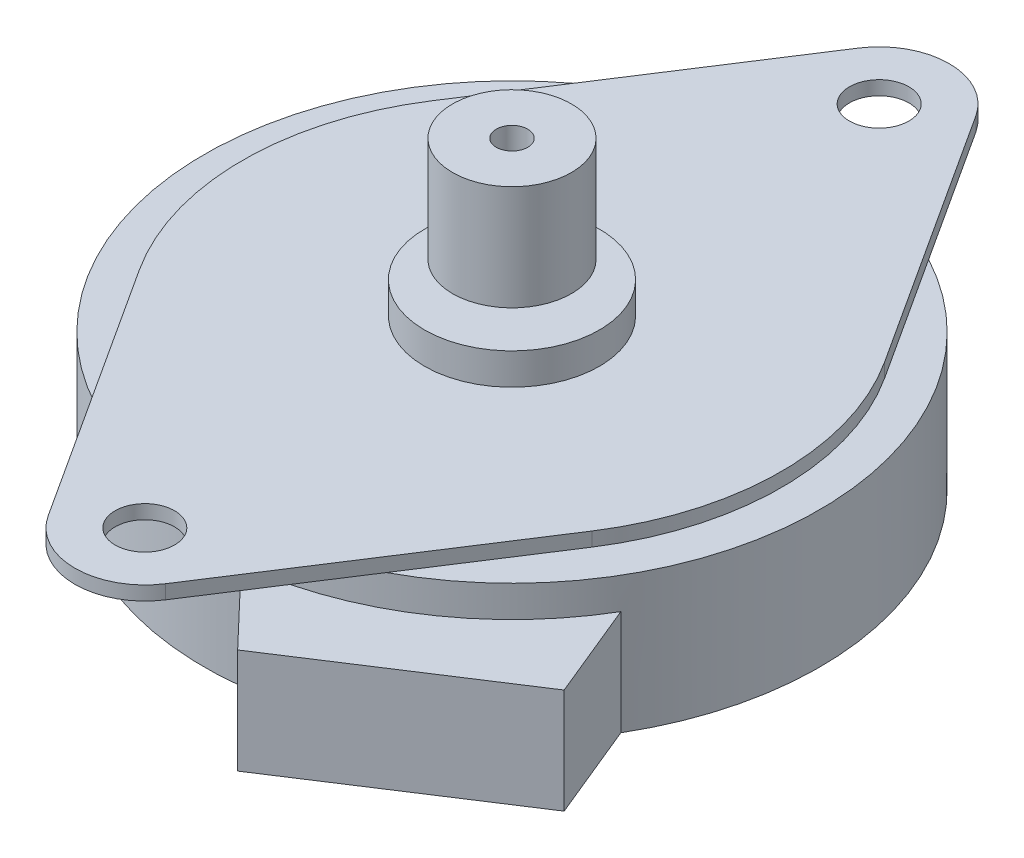
SolidWorks part; units mm, degrees
ref_plane "Piano frontale" through (0, 0, 0) normal (0, 0, 1) x (1, 0, 0)
ref_plane "Piano superiore" through (0, 0, 0) normal (0, 1, 0) x (1, 0, 0)
ref_plane "Piano destro" through (0, 0, 0) normal (1, 0, 0) x (0, 0, -1)
sketch "Schizzo1" plane through (0, 0, 0) normal (0, 1, 0) x (1, 0, 0)
  circle A0 centre (0, 0) radius 17.6
  dimension "D1" = 35.2
extrude "Estrusione-Estrusione1" add sketch "Schizzo1" along normal blind 7.8
sketch "Schizzo2" plane through (0, 7.8, 0) normal (0, 1, 0) x (1, 0, 0)
  line L0 (0, 19.0061) -> (0, -19.0061) construction
  line L1 (-3.3578, -23.1737) -> (-12.9377, -8.3755)
  line L2 (3.3578, -23.1737) -> (12.9377, -8.3755)
  line L3 (3.3578, 23.1737) -> (12.9377, 8.3755)
  line L4 (-3.3578, 23.1737) -> (-12.9377, 8.3755)
  circle A0 centre (0, 21) radius 1.7
  arc A1 (3.3578, 23.1737) -> (-3.3578, 23.1737) centre (0, 21) ccw
  arc A2 (-12.9377, 8.3755) -> (-12.9377, -8.3755) centre (0, 0) ccw
  circle A3 centre (0, -21) radius 1.7
  arc A4 (-3.3578, -23.1737) -> (3.3578, -23.1737) centre (0, -21) ccw
  arc A5 (12.9377, -8.3755) -> (12.9377, 8.3755) centre (0, 0) ccw
  point P18 (0, 0)
  dimension "D2" = 3.4
  dimension "D3" = 8
  dimension "D1" = 21
  dimension "D4" = 2
extrude "Estrusione-Estrusione2" add sketch "Schizzo2" along normal blind 0.8
sketch "Schizzo3" plane through (0, 8.6, 0) normal (0, 1, 0) x (1, 0, 0)
  circle A0 centre (0, 0) radius 5
  dimension "D1" = 10
extrude "Estrusione-Estrusione3" add sketch "Schizzo3" along normal blind 1.8
sketch "Schizzo4" plane through (0, 10.4, 0) normal (0, 1, 0) x (1, 0, 0)
  circle A0 centre (0, 0) radius 0.9
  dimension "D1" = 1.8
extrude "Estrusione-Estrusione4" add sketch "Schizzo4" along normal blind 5
sketch "Schizzo5" plane through (0, 0, 0) normal (0, -1, 0) x (1, 0, 0)
  circle A0 centre (0, 0) radius 2.6
  dimension "D1" = 5.2
extrude "Estrusione-Estrusione5" add sketch "Schizzo5" along normal blind 0.5
sketch "Schizzo6" plane through (0, 0, 0) normal (0, -1, 0) x (1, 0, 0)
  line L0 (0, 0) -> (9.584, 14.7617) construction
  line L1 (6.1007, 21.7923) -> (17.4236, 14.441)
  line L5 (9.584, 14.7617) -> (11.7621, 18.1166) construction
  line L7 (6.1007, 21.7923) -> (1.9938, 17.4867)
  line L8 (17.4236, 14.441) -> (15.1619, 8.9374)
  arc A0 (1.9938, 17.4867) -> (15.1619, 8.9374) centre (0, 0) cw
  circle A1 centre (0, 0) radius 17.6 construction
  dimension "D1" = 13.5
  dimension "D2" = 15.7
  dimension "D3" = 4
extrude "Estrusione-Estrusione6" add sketch "Schizzo6" against normal blind 6
sketch "Эскиз1" plane through (0, 10.4, 0) normal (0, 1, 0) x (1, 0, 0)
  circle A0 centre (0, 0) radius 0.9
  circle A1 centre (0, 0) radius 3.4
  dimension "D1" = 6.8
extrude "Бобышка-Вытянуть1" add sketch "Эскиз1" along normal blind 6 from offset 1
